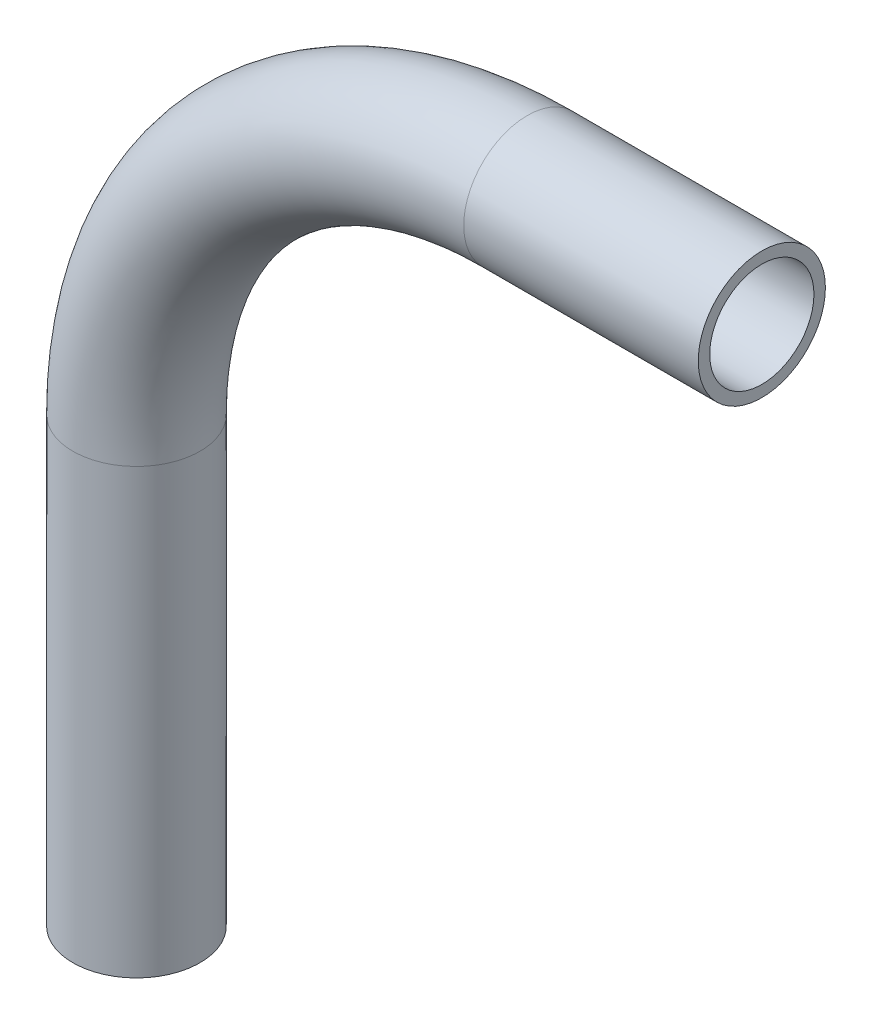
SolidWorks part; units mm, degrees
material "6061-T6 (SS)"
ref_plane "Front Plane" through (0, 0, 0) normal (0, 0, 1) x (1, 0, 0)
ref_plane "Top Plane" through (0, 0, 0) normal (0, 1, 0) x (1, 0, 0)
ref_plane "Right Plane" through (0, 0, 0) normal (1, 0, 0) x (0, 0, -1)
sketch "Sketch1" plane through (0, 0, 0) normal (0, 0, 1) x (1, 0, 0)
  line L0 (0, -23.8125) -> (0, -50.8)
  line L1 (23.8125, 0) -> (38.1, 0)
  arc A0 (0, -23.8125) -> (23.8125, 0) centre (23.8125, -23.8125) cw
  point P6 (0, 0)
  dimension "D3" = 23.8125
  dimension "D1" = 50.8
  dimension "D2" = 38.1
  dimension "D4" = 90
ref_plane "Plane1" through (38.1, 0, 0) normal (1, 0, 0) x (0, 0, -1)
sketch "Sketch2" plane through (38.1, 0, 0) normal (1, 0, 0) x (0, 0, -1)
  circle A0 centre (0, 0) radius 3.175
  circle A1 centre (0, 0) radius 3.8735
  dimension "D1" = 6.35
  dimension "D2" = 7.747
sweep "Sweep1" add profiles "Sketch2" path "Sketch1"
